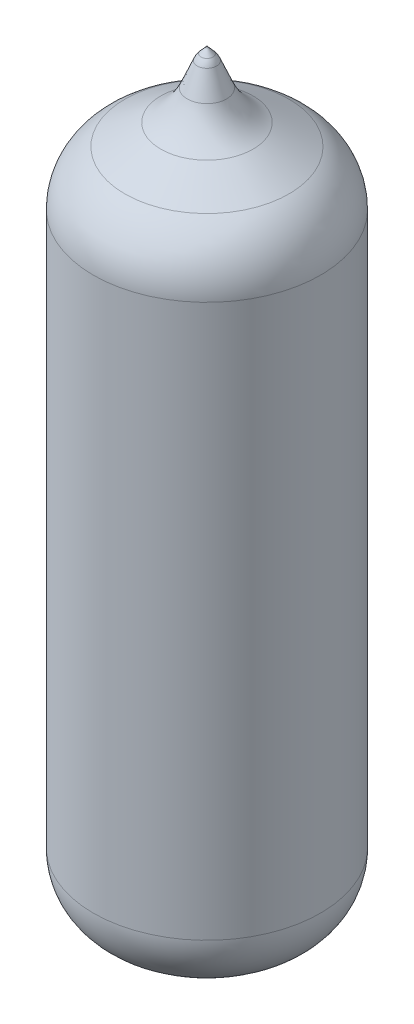
SolidWorks part; units mm, degrees
material "Verre"
ref_plane "Plan de face" through (0, 0, 0) normal (0, 0, 1) x (1, 0, 0)
ref_plane "Plan de dessus" through (0, 0, 0) normal (0, 1, 0) x (1, 0, 0)
ref_plane "Plan de droite" through (0, 0, 0) normal (1, 0, 0) x (0, 0, -1)
sketch "Esquisse1" plane through (0, 0, 0) normal (0, 0, 1) x (1, 0, 0)
  line L0 (0, 0) -> (0, 36) construction
  line L1 (0, 0) -> (-5.4, 0) construction
  line L2 (0, 0) -> (0, 30.9941) construction
  line L3 (-3.9024, 31.8606) -> (-2.1938, 32.8492)
  line L4 (0, 0) -> (-2.4, 0)
  line L5 (-0.9304, 34.2838) -> (-0.4595, 35.4049)
  line L6 (-0.2824, 35.6848) -> (0, 36)
  line L7 (-5.4, 3) -> (-5.4, 29.2639)
  line L8 (0, 36) -> (0, 0)
  arc A0 (-5.4, 3) -> (-2.4, 0) centre (-2.4, 3) ccw
  arc A1 (-2.1938, 32.8492) -> (-0.9304, 34.2838) centre (-3.6963, 35.4459) ccw
  arc A2 (-3.9024, 31.8606) -> (-5.4, 29.2639) centre (-2.4, 29.2639) ccw
  arc A3 (-0.4595, 35.4049) -> (-0.2824, 35.6848) centre (0.4625, 35.0175) cw
  dimension "D3" = 3
  dimension "D4" = 1
  dimension "D1" = 36
  dimension "D2" = 5.4
revolve "Révolution1" add sketch "Esquisse1" angle 360 about L8
ref_plane "Position chiffres" through (0, 0, 0) normal (0, 0, 1) x (1, 0, 0)
